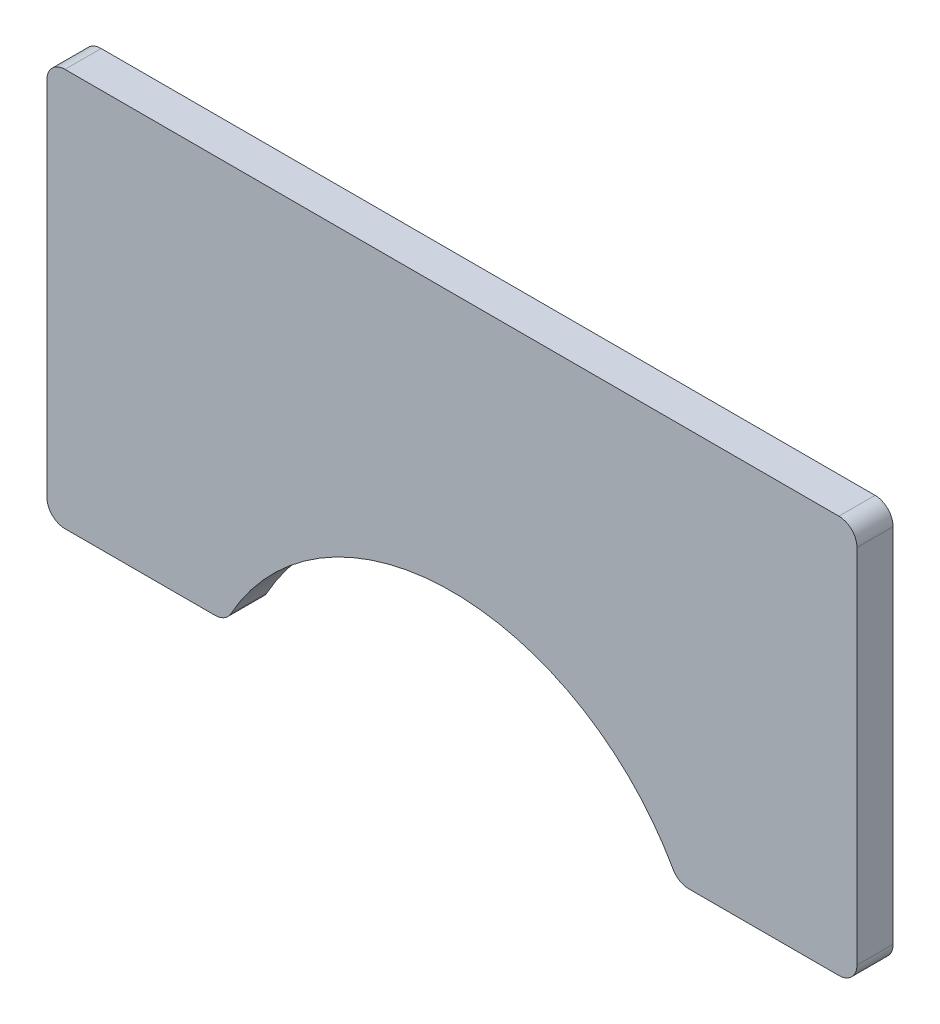
SolidWorks part; units mm, degrees
ref_plane "Front Plane" through (0, 0, 0) normal (0, 0, 1) x (1, 0, 0)
ref_plane "Top Plane" through (0, 0, 0) normal (0, 1, 0) x (1, 0, 0)
ref_plane "Right Plane" through (0, 0, 0) normal (1, 0, 0) x (0, 0, -1)
sketch "Sketch1" plane through (0, 0, 0) normal (0, 0, 1) x (1, 0, 0)
  line L1 (-28.448, -13.97) -> (28.448, -13.97)
  line L2 (-28.448, -13.97) -> (-28.448, 13.97)
  line L3 (-28.448, 13.97) -> (28.448, 13.97)
  line L4 (28.448, -13.97) -> (28.448, 13.97)
  line L5 (-28.448, -13.97) -> (28.448, 13.97) construction
  line L6 (-28.448, 13.97) -> (28.448, -13.97) construction
  point P0 (0, 0)
  dimension "D1" = 27.94
  dimension "D2" = 56.896
extrude "Boss-Extrude1" add sketch "Sketch1" along normal blind 2.54
sketch "Sketch2" plane through (0, 0, 2.54) normal (0, 0, 1) x (1, 0, 0)
  line L0 (-28.448, -13.97) -> (28.448, -13.97) construction
  line L1 (-15.875, -13.97) -> (15.875, -13.97)
  arc A0 (-15.875, -13.97) -> (15.875, -13.97) centre (0, -21.977) cw
  point P3 (0, -4.197)
  dimension "D1" = 17.78
  dimension "D2" = 31.75
extrude "Cut-Extrude1" cut sketch "Sketch2" against normal through all
fillet "Fillet1" radius 1.27 6 edges at (-28.448, -13.97, 1.27) (28.448, -13.97, 1.27) (28.448, 13.97, 1.27) (-28.448, 13.97, 1.27) (-15.875, -13.97, 1.27) (15.875, -13.97, 1.27)
sketch "Sketch4" plane through (0, 0, 0) normal (1, 0, 0) x (0, 0, -1)
  line L0 (0, 6.604) -> (9.652, 6.604)
  line L1 (0, -12.7) -> (0, 12.7) construction
  line L2 (9.652, 6.604) -> (9.652, -6.604)
  line L3 (9.652, -6.604) -> (0, -6.604)
  line L4 (0, -6.604) -> (0, -4.064)
  line L5 (0, -4.064) -> (7.112, -4.064)
  line L6 (7.112, -4.064) -> (7.112, 4.064)
  line L7 (7.112, 4.064) -> (0, 4.064)
  line L8 (0, 4.064) -> (0, 6.604)
  line L9 (0, 6.604) -> (0, 4.064)
  line L10 (0, -4.064) -> (0, -6.604)
  point P6 (3.556, 4.064)
  point P11 (7.112, 0)
  dimension "D1" = 2.54
  dimension "D2" = 2.54
  dimension "D3" = 2.54
  dimension "D4" = 7.112
  dimension "D5" = 8.128
